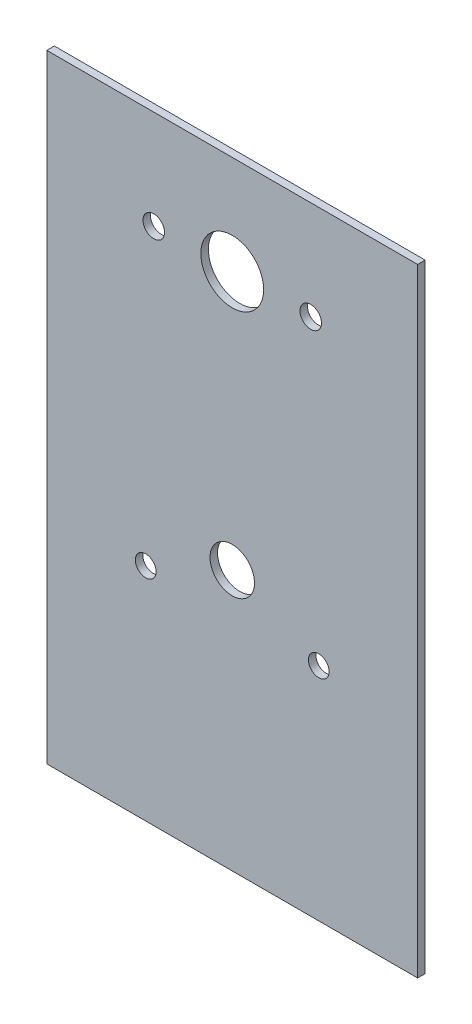
SolidWorks part; units mm, degrees
ref_plane "Front Plane" through (0, 0, 0) normal (0, 0, 1) x (1, 0, 0)
ref_plane "Top Plane" through (0, 0, 0) normal (0, 1, 0) x (1, 0, 0)
ref_plane "Right Plane" through (0, 0, 0) normal (1, 0, 0) x (0, 0, -1)
sketch "Sketch1" plane through (0, 0, 0) normal (0, 0, 1) x (1, 0, 0)
  line L1 (-37.5, 20) -> (37.5, 20)
  line L2 (-37.5, 20) -> (-37.5, -105)
  line L3 (-37.5, -105) -> (37.5, -105)
  line L4 (37.5, 20) -> (37.5, -105)
  line L5 (0, -105) -> (0, 20) construction
  line L6 (-37.5, -42.5) -> (37.5, -42.5) construction
  circle A0 centre (15.875, 0) radius 2.1828 construction
  circle A1 centre (-15.875, 0) radius 2.1828 construction
  circle A2 centre (17.5, -60.2991) radius 2.1 construction
  circle A3 centre (-17.5, -60.2991) radius 2.1 construction
  circle A4 centre (15.875, 0) radius 2.1828
  circle A5 centre (-15.875, 0) radius 2.1828
  circle A6 centre (17.5, -60.2991) radius 2.1
  circle A7 centre (-17.5, -60.2991) radius 2.1
  circle A8 centre (0, 0) radius 6.35 construction
  circle A9 centre (0, 0) radius 6.35
  circle A10 centre (0, -52.2991) radius 4.5 construction
  circle A11 centre (0, -52.2991) radius 4.5
  point P108 (0, -42.5)
  dimension "D1" = 75
  dimension "D2" = 125
  dimension "D3" = 20
extrude "Boss-Extrude1" add sketch "Sketch1" along normal blind 1.524 contours L4 L1 L2 L3 A11 A9 A7 A6 A5 A4
